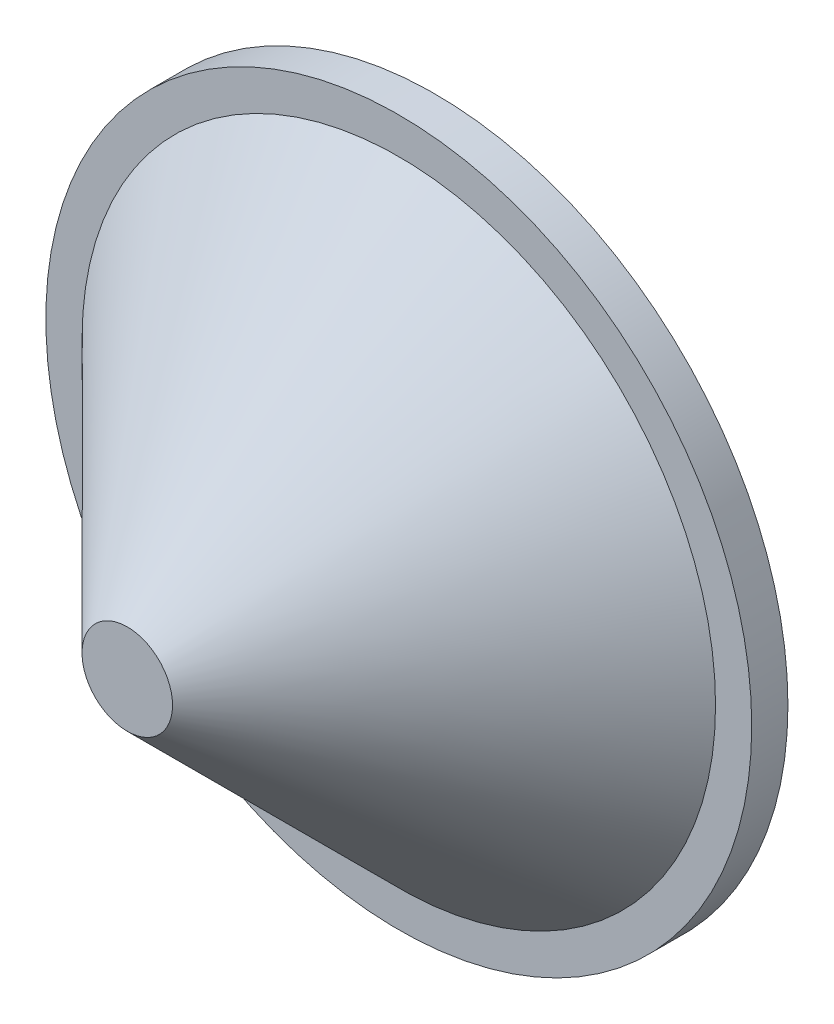
SolidWorks part; units mm, degrees
material "AISI 1020"
ref_plane "Спереди" through (0, 0, 0) normal (0, 0, 1) x (1, 0, 0)
ref_plane "Сверху" through (0, 0, 0) normal (0, 1, 0) x (1, 0, 0)
ref_plane "Справа" through (0, 0, 0) normal (1, 0, 0) x (0, 0, -1)
sketch "Эскиз1" plane through (0, 0, 0) normal (1, 0, 0) x (0, 0, -1)
  line L0 (-926.8021, 0) -> (49073.1979, 0) construction
  line L2 (0, 0) -> (0, 39)
  line L3 (0, 39) -> (-4, 39)
  line L4 (-4, 39) -> (-4, 35)
  line L5 (-4, 35) -> (-34, 5)
  line L6 (-34, 5) -> (-34, 0)
  line L7 (0, 0) -> (-34, 0)
  point P5 (-4, 37)
  dimension "D1" = 45
  dimension "D2" = 4
  dimension "D3" = 10
  dimension "D4" = 4
  dimension "D5" = 30
revolve "Повернуть1" add sketch "Эскиз1" angle 360 about L0
sketch "Эскиз2" plane through (0, 0, 0) normal (0, 0, -1) x (-1, 0, 0)
  line L0 (12.5, -15.5) -> (-12.5, -15.5) construction
  line L1 (-15.5, -12.5) -> (-15.5, 12.5) construction
  line L2 (-12.5, 15.5) -> (12.5, 15.5) construction
  line L3 (15.5, 12.5) -> (15.5, -12.5) construction
  line L4 (12.5, -15.5) -> (-12.5, -15.5)
  line L5 (-15.5, -12.5) -> (-15.5, 12.5)
  line L6 (-12.5, 15.5) -> (12.5, 15.5)
  line L7 (15.5, 12.5) -> (15.5, -12.5)
  line L8 (-15.5, -12.5) -> (-12.5, -15.5)
  line L9 (12.5, -15.5) -> (15.5, -12.5)
  line L10 (15.5, 12.5) -> (12.5, 15.5)
  line L11 (-12.5, 15.5) -> (-15.5, 12.5)
extrude "Бобышка-Вытянуть1" add sketch "Эскиз2" along normal blind 5
